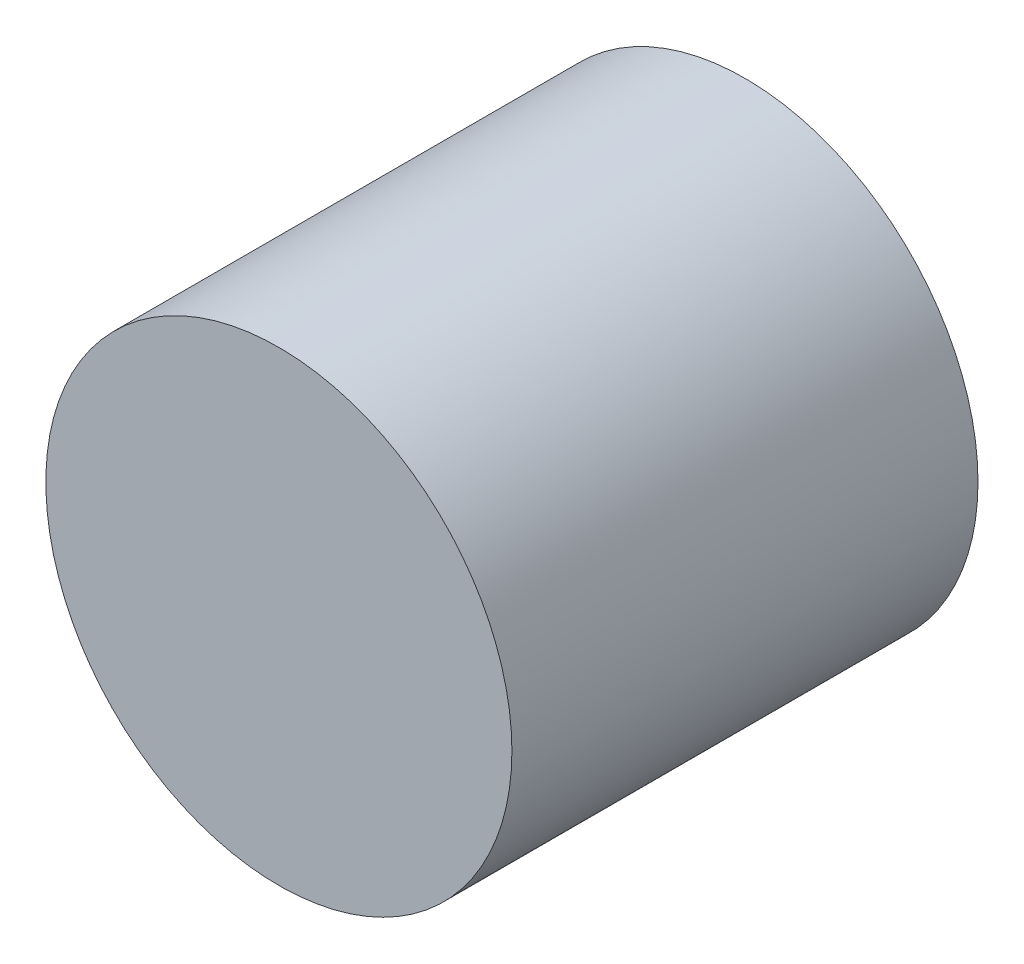
SolidWorks part; units mm, degrees
ref_plane "Front Plane" through (0, 0, 0) normal (0, 0, 1) x (1, 0, 0)
ref_plane "Top Plane" through (0, 0, 0) normal (0, 1, 0) x (1, 0, 0)
ref_plane "Right Plane" through (0, 0, 0) normal (1, 0, 0) x (0, 0, -1)
sketch "Sketch1" plane through (0, 0, 0) normal (0, 0, 1) x (1, 0, 0)
  circle A0 centre (0, 0) radius 3.5
  dimension "D1" = 7
extrude "Boss-Extrude1" add sketch "Sketch1" along normal blind 7
sketch "Sketch2" plane through (0, 0, 0) normal (0, 0, -1) x (-1, 0, 0)
  circle A0 centre (0, 0) radius 2.75
  dimension "D1" = 5.5
extrude "Cut-Extrude1" cut sketch "Sketch2" against normal blind 4.5
